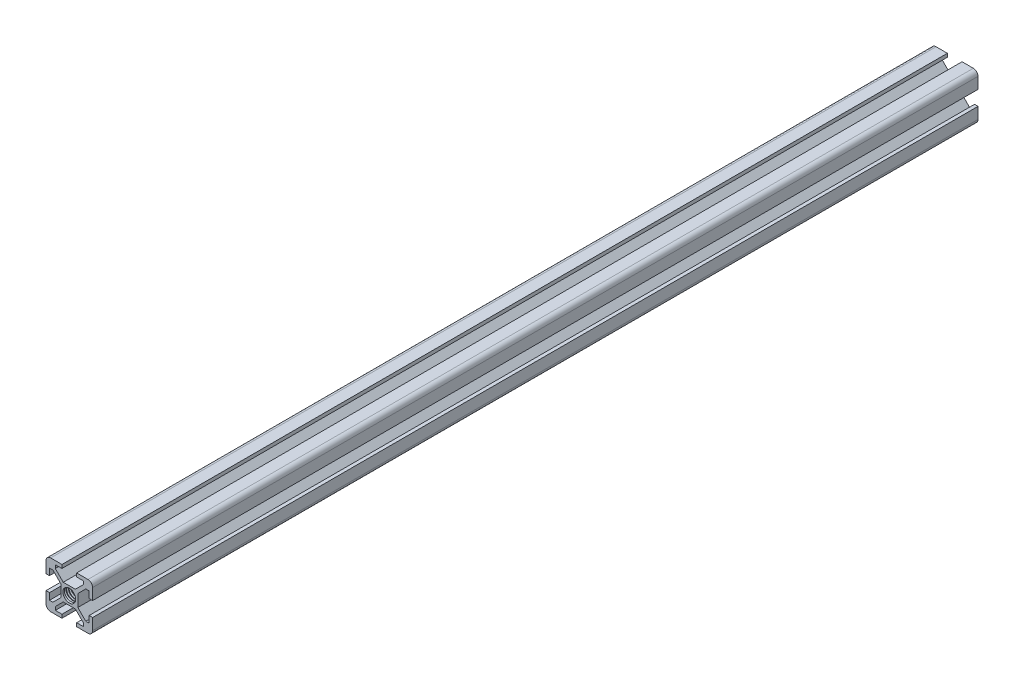
SolidWorks part; units mm, degrees
material "1060 Alloy"
ref_plane "Front Plane" through (0, 0, 0) normal (0, 0, 1) x (1, 0, 0)
ref_plane "Top Plane" through (0, 0, 0) normal (0, 1, 0) x (1, 0, 0)
ref_plane "Right Plane" through (0, 0, 0) normal (1, 0, 0) x (0, 0, -1)
sketch "Sketch1" plane through (0, 0, 0) normal (0, 0, 1) x (1, 0, 0)
  line L0 (0, 0) -> (3.66, 3.66) construction
  line L1 (-2.5993, -3.66) -> (2.5993, -3.66)
  line L2 (-3.66, -2.5993) -> (-3.66, 2.5993)
  line L3 (-2.5993, 3.66) -> (2.5993, 3.66)
  line L4 (3.66, -2.5993) -> (3.66, 2.5993)
  line L5 (-3.66, -3.66) -> (3.66, 3.66) construction
  line L6 (-3.66, 3.66) -> (3.66, -3.66) construction
  line L7 (-8, -10) -> (-3.15, -10)
  line L8 (-10, -8) -> (-10, -3.15)
  line L9 (-8, 10) -> (-3.15, 10)
  line L10 (10, -8) -> (10, -3.15)
  line L11 (-10, -10) -> (3.66, 3.66) construction
  line L12 (-10, 10) -> (9.4142, -9.4142) construction
  line L13 (0.5303, -0.5303) -> (1.0607, 0) construction
  line L14 (-0.5303, 0.5303) -> (0, 1.0607) construction
  line L15 (-0.5303, 0.5303) -> (9.4697, 10.5303) construction
  line L16 (0.5303, -0.5303) -> (10.5303, 9.4697) construction
  line L17 (0, 0) -> (10, 0) construction
  line L18 (-10, -3.15) -> (-8.5, -3.15)
  line L19 (8.5, 3.15) -> (8.5, 5.995)
  line L20 (10, 3.15) -> (10, 8)
  line L21 (8.5, 5.995) -> (7.0557, 5.995)
  line L22 (9.4142, 9.4142) -> (10, 10) construction
  line L23 (0, 0) -> (10, 10) construction
  line L24 (9.4142, 9.4142) -> (10, 10) construction
  line L25 (0, 14.5751) -> (0, -10) construction
  line L26 (0, 0) -> (11.8172, 11.8172) construction
  line L27 (3.15, 10) -> (8, 10)
  line L28 (5.995, 8.5) -> (5.995, 7.0557)
  line L29 (10, 3.15) -> (8.5, 3.15)
  line L30 (3.15, 8.5) -> (5.995, 8.5)
  line L31 (9.8413, 8.7807) -> (10, 8.9393)
  line L32 (8.7807, 9.8413) -> (8.9393, 10)
  line L33 (0.5303, 0.5303) -> (1.0607, 0) construction
  line L34 (-0.5303, -0.5303) -> (0, -1.0607) construction
  line L35 (5.995, -8.5) -> (5.995, -7.0557)
  line L36 (3.15, -8.5) -> (5.995, -8.5)
  line L38 (-8, -10) -> (-3.15, -10)
  line L39 (8.5, -5.995) -> (7.0557, -5.995)
  line L40 (8.5, -3.15) -> (8.5, -5.995)
  line L42 (10, -3.15) -> (10, -8)
  line L43 (-8.5, -5.995) -> (-7.0557, -5.995)
  line L44 (-8.5, -3.15) -> (-8.5, -5.995)
  line L45 (-10, 3.15) -> (-8.5, 3.15)
  line L46 (-10, -8) -> (-10, -3.15)
  line L47 (8, -10) -> (3.15, -10)
  line L48 (10, -3.15) -> (8.5, -3.15)
  line L49 (-3.15, -8.5) -> (-5.995, -8.5)
  line L50 (-0.5303, 0.5303) -> (-1.0607, 0) construction
  line L51 (0.5303, -0.5303) -> (0, -1.0607) construction
  line L52 (-5.995, -8.5) -> (-5.995, -7.0557)
  line L53 (-10, 3.15) -> (-10, 8)
  line L54 (3.15, -10) -> (3.15, -8.5)
  line L55 (-8.5, 5.995) -> (-7.0557, 5.995)
  line L56 (-8.5, 3.15) -> (-8.5, 5.995)
  line L57 (-0.5303, -0.5303) -> (-1.0607, 0) construction
  line L58 (0.5303, 0.5303) -> (0, 1.0607) construction
  line L59 (-5.995, 8.5) -> (-5.995, 7.0557)
  line L60 (-3.15, 8.5) -> (-5.995, 8.5)
  line L61 (-3.15, -10) -> (-3.15, -8.5)
  line L62 (8, 10) -> (3.15, 10)
  line L63 (-10, 3.15) -> (-10, 8)
  line L64 (3.15, -10) -> (8, -10)
  line L65 (3.15, -10) -> (8, -10)
  line L66 (-3.15, -10) -> (-8, -10)
  line L67 (-2.5993, 3.66) -> (-5.995, 7.0557)
  line L68 (-3.66, 2.5993) -> (-7.0557, 5.995)
  line L69 (-3.66, -2.5993) -> (-7.0557, -5.995)
  line L70 (-2.5993, -3.66) -> (-5.995, -7.0557)
  line L71 (2.5993, -3.66) -> (5.995, -7.0557)
  line L72 (3.66, -2.5993) -> (7.0557, -5.995)
  line L73 (3.66, 2.5993) -> (7.0557, 5.995)
  line L74 (2.5993, 3.66) -> (5.995, 7.0557)
  line L75 (3.15, 10) -> (8, 10)
  line L76 (-3.15, 10) -> (-8, 10)
  line L78 (3.15, 10) -> (3.15, 8.5)
  line L79 (-3.15, 10) -> (-3.15, 8.5)
  circle A0 centre (0, 0) radius 2.75
  arc A1 (8, 10) -> (10, 8) centre (8, 8) cw
  arc A2 (8, -10) -> (10, -8) centre (8, -8) ccw
  arc A3 (-8, -10) -> (-10, -8) centre (-8, -8) cw
  arc A4 (-8, 10) -> (-10, 8) centre (-8, 8) ccw
  dimension "D1" = 5.5
  dimension "D6" = 2
  dimension "D2" = 7.32
  dimension "D3" = 20
  dimension "D7" = 2.845
  dimension "D9" = 20
  dimension "D12" = 1.4443
  dimension "D13" = 7.32
  dimension "D14" = 3.66
  dimension "D4" = 3.15
  dimension "D5" = 1.5
  dimension "D15" = 4.85
  dimension "D16" = 5.1987
  dimension "D17" = 3.66
  dimension "D18" = 2.845
  dimension "D19" = 6.3
extrude "Boss-Extrude1" add sketch "Sketch1" along normal blind 380 contours L9 A4 L53 L45 L56 L55 L68 L2 L69 L43 L44 L18 L8 A3 L7 L61 L49 L52 L70 L1 L71 L35 L36 L54 L47 A2 L10 L48 L40 L39 L72 L4 L73 L21 L19 L29 L20 A1 L27 L78 L30 L28 L74 L3 L67 L59 L60 L79
ref_plane "Plane1" through (0, 0, 1.2) normal (0, 0, -1) x (-1, 0, 0)
sketch "Sketch2" plane through (0, 0, 1.2) normal (0, 0, -1) x (-1, 0, 0)
  circle A0 centre (0, 0) radius 2.15
curve "Helix/Spiral1" pitch 1 height 18.5 turns 18.5
sketch "Sketch3" plane through (0, 0, 0) normal (1, 0, 0) x (0, 0, -1)
  line L0 (-2.2297, 2.75) -> (-0.75, 2.75) construction
  line L1 (0, 2.75) -> (-380, 2.75) construction
  line L2 (-0.75, 3.3895) -> (-1.125, 2.74)
  line L3 (-1.125, 2.74) -> (-0.375, 2.74)
  line L4 (-0.375, 2.74) -> (-0.75, 3.3895)
  line L5 (0, -2.5993) -> (0, 2.5993) construction
  circle A0 centre (-0.75, 2.9565) radius 0.2165 construction
  dimension "D1" = 0.75
  dimension "D2" = 0.75
  dimension "D3" = 0.01
  dimension "D4" = 0
sweep "Cut-Sweep2" cut profiles "Sketch3" path "Helix/Spiral1"
ref_plane "Plane2" through (0, 0, 190) normal (0, 0, -1) x (-1, 0, 0)
mirror "Mirror1" about plane through (0, 0, 190) normal (0, 0, -1) of "Cut-Sweep2"
